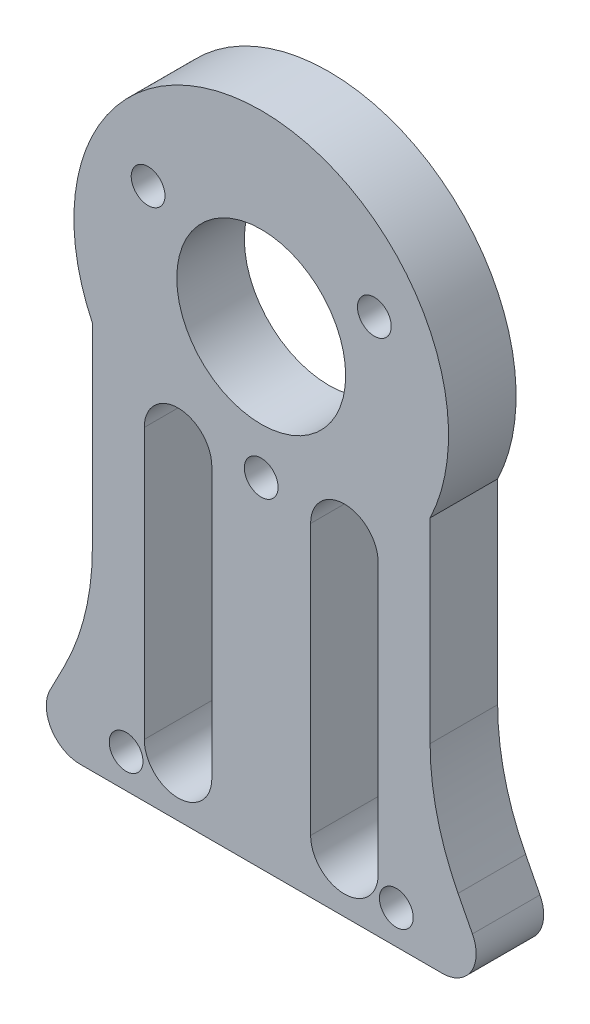
SolidWorks part; units mm, degrees
material "1060 Alloy"
ref_plane "Front Plane" through (0, 0, 0) normal (0, 0, 1) x (1, 0, 0)
ref_plane "Top Plane" through (0, 0, 0) normal (0, 1, 0) x (1, 0, 0)
ref_plane "Right Plane" through (0, 0, 0) normal (1, 0, 0) x (0, 0, -1)
sketch "Sketch2" plane through (0, 0, 0) normal (0, 0, 1) x (1, 0, 0)
  line L0 (10, -4.798) -> (10, -16.3754)
  line L2 (-10, -4.798) -> (-10, -16.3754)
  line L3 (-11.655, -23.2246) -> (-12.5048, -24.8804)
  line L4 (-10.7255, -27.7936) -> (10.7255, -27.7936)
  line L5 (12.5048, -24.8804) -> (11.655, -23.2246)
  line L6 (-4.9243, -8.6221) -> (-4.9243, -24.6221) construction
  line L7 (-2.9243, -8.6221) -> (-2.9243, -24.6221)
  line L8 (-6.9243, -8.6221) -> (-6.9243, -24.6221)
  line L9 (4.9243, -8.6221) -> (4.9243, -24.6221) construction
  line L10 (2.9243, -8.6221) -> (2.9243, -24.6221)
  line L11 (6.9243, -8.6221) -> (6.9243, -24.6221)
  arc A0 (10, -4.798) -> (-10, -4.798) centre (0, 0) ccw
  arc A1 (10, -16.3754) -> (11.655, -23.2246) centre (25, -16.3754) ccw
  arc A2 (-11.655, -23.2246) -> (-10, -16.3754) centre (-25, -16.3754) ccw
  arc A3 (12.5048, -24.8804) -> (10.7255, -27.7936) centre (10.7255, -25.7936) cw
  arc A4 (-10.7255, -27.7936) -> (-12.5048, -24.8804) centre (-10.7255, -25.7936) cw
  circle A5 centre (-8, -25.7936) radius 1
  circle A6 centre (8, -25.7936) radius 1
  circle A7 centre (0, 0) radius 5
  arc A8 (-2.9243, -8.6221) -> (-6.9243, -8.6221) centre (-4.9243, -8.6221) ccw
  arc A9 (-6.9243, -24.6221) -> (-2.9243, -24.6221) centre (-4.9243, -24.6221) ccw
  arc A10 (2.9243, -8.6221) -> (6.9243, -8.6221) centre (4.9243, -8.6221) cw
  arc A11 (6.9243, -24.6221) -> (2.9243, -24.6221) centre (4.9243, -24.6221) cw
  circle A12 centre (0, -7.7339) radius 1
  circle A13 centre (-6.6978, 3.8669) radius 1
  circle A14 centre (6.6978, 3.8669) radius 1
  point P12 (10, -20)
  point P15 (-10, -20)
  point P18 (14, -27.7936)
  point P21 (-14, -27.7936)
  point P28 (-4.9243, -16.6221)
  point P38 (4.9243, -16.6221)
  point P47 (0, 0)
  dimension "D1" = 10
  dimension "D3" = 2
  dimension "D5" = 15
  dimension "D6" = 2
  dimension "D9" = 3
  dimension "D2" = 20
  dimension "D4" = 28
  dimension "D7" = 2
  dimension "D8" = 2
extrude "Boss-Extrude1" add sketch "Sketch2" along normal blind 4
